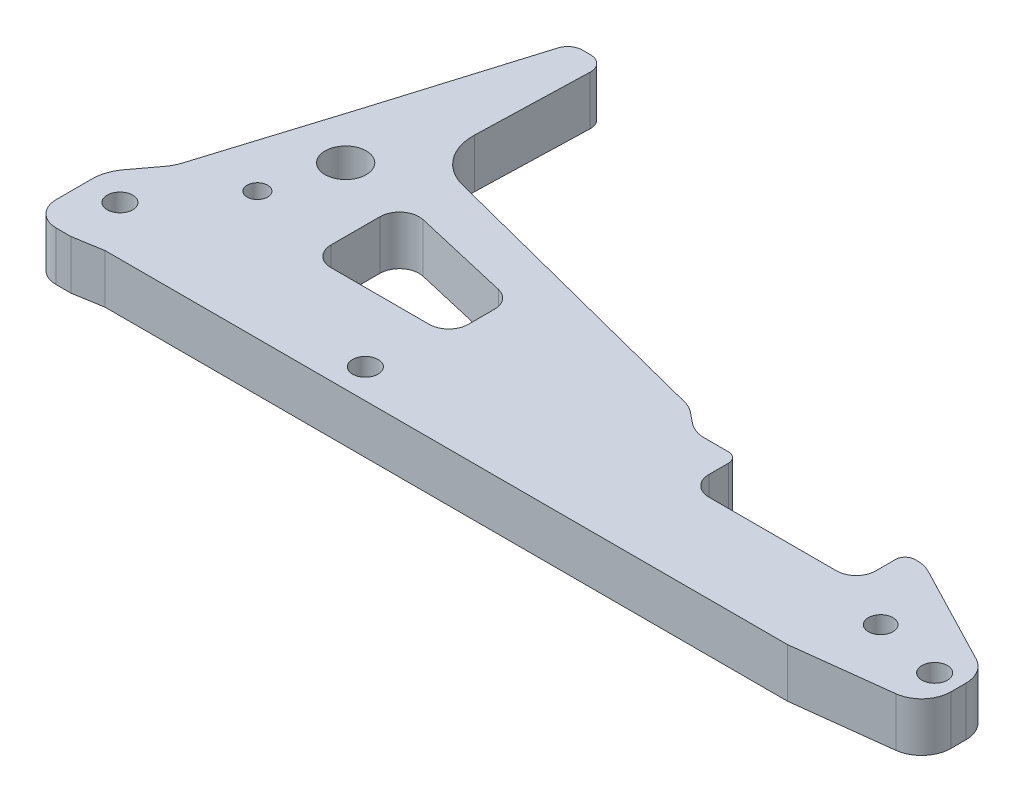
SolidWorks part; units mm, degrees
material "PE High Density"
ref_plane "Front Plane" through (0, 0, 0) normal (0, 0, 1) x (1, 0, 0)
ref_plane "Top Plane" through (0, 0, 0) normal (0, 1, 0) x (1, 0, 0)
ref_plane "Right Plane" through (0, 0, 0) normal (1, 0, 0) x (0, 0, -1)
sketch "Sketch1" plane through (0, 0, 0) normal (0, 1, 0) x (1, 0, 0)
  line L0 (164, 15) -> (139, 28)
  line L5 (164, 3) -> (139, 0)
  line L7 (-14, 14) -> (-14, 2)
  line L9 (0, 0) -> (139, 0)
  line L10 (164, 3) -> (164, 15)
  line L13 (92, 28) -> (139, 28)
  line L15 (1, 51) -> (11, 84)
  line L16 (11, 84) -> (18, 84)
  line L18 (-14, 2) -> (-14, -1)
  line L19 (-14, -1) -> (-6, -1)
  line L22 (-6, -1) -> (0, 0)
  line L23 (17, 50) -> (87, 32)
  line L24 (87, 32) -> (92, 28)
  line L25 (18, 84) -> (17, 50)
  line L26 (-14, 14) -> (-8, 22)
  line L27 (-8, 22) -> (1, 51)
  circle A0 centre (-7, 10) radius 2.6
  circle A3 centre (159, 10) radius 2.6
  circle A4 centre (5, 26) radius 2.1
  circle A6 centre (9, 40) radius 4.2
  circle A8 centre (145, 13) radius 2.5
  dimension "D9" = 5.2
  dimension "D12" = 5
  dimension "D15" = 16
  dimension "D13" = 5.2
  dimension "D17" = 4.2
  dimension "D20" = 6
  dimension "D23" = 8.4
  dimension "D27" = 10
  dimension "D3" = 44
  dimension "D4" = 3
  dimension "D5" = 25
  dimension "D6" = 25
  dimension "D7" = 166
  dimension "D8" = 12
  dimension "D10" = 7
  dimension "D11" = 8
  dimension "D14" = 40
  dimension "D16" = 5
  dimension "D18" = 7
  dimension "D19" = 12
  dimension "D21" = 10
  dimension "D22" = 75
  dimension "D24" = 18
  dimension "D25" = 15
  dimension "D26" = 16
  dimension "D28" = 12
  dimension "D29" = 10
  dimension "D30" = 3
  dimension "D31" = 8
  dimension "D32" = 70
  dimension "D33" = 16
  dimension "D34" = 14
  dimension "D35" = 6
  dimension "D36" = 8
  dimension "D37" = 29
  dimension "D38" = 4
  dimension "D39" = 28
  dimension "D40" = 13
extrude "Boss-Extrude1" add sketch "Sketch1" along normal blind 10
fillet "Fillet2" radius 6 3 edges at (164, 5, -3) (164, 5, -15) (139, 5, -28)
fillet "Fillet3" radius 3 2 edges at (11, 5, -84) (18, 5, -84)
sketch "Sketch4" plane through (0, 10, 0) normal (0, 1, 0) x (1, 0, 0)
  line L0 (22, 39) -> (22, 20)
  line L6 (22, 39) -> (50, 32.5)
  line L7 (50, 32.5) -> (50, 20)
  line L21 (50, 20) -> (22, 20)
  circle A0 centre (9, 40) radius 4.2 construction
  dimension "D1" = 13
  dimension "D2" = 1
  dimension "D3" = 19
  dimension "D5" = 28
  dimension "D8" = 12.5
extrude "Cut-Extrude1" cut sketch "Sketch4" against normal through all
sketch "Sketch7" plane through (0, 10, 0) normal (0, 1, 0) x (1, 0, 0)
  circle A0 centre (47, 6) radius 2.6
  circle A1 centre (9, 40) radius 4.2 construction
  dimension "D3" = 5.2
  dimension "D1" = 6
  dimension "D2" = 38
extrude "Cut-Extrude4" cut sketch "Sketch7" against normal through all
fillet "Fillet8" radius 5 1 edges at (-14, 5, 1)
fillet "Fillet9" radius 4 4 edges at (22, 5, -20) (50, 5, -32.5) (22, 5, -39) (50, 5, -20)
sketch "Sketch10" plane through (0, 10, 0) normal (0, 1, 0) x (1, 0, 0)
  line L0 (101, 28) -> (101, 18)
  line L1 (137.5332, 28) -> (92, 28) construction
  line L2 (101, 18) -> (135, 18)
  line L3 (135, 18) -> (135, 28)
  line L4 (135, 28) -> (101, 28)
  circle A0 centre (9, 40) radius 4.2 construction
  dimension "D3" = 92
  dimension "D1" = 10
  dimension "D2" = 0
  dimension "D4" = 34
extrude "Cut-Extrude6" cut sketch "Sketch10" against normal through all
fillet "Fillet10" radius 4 2 edges at (135, 5, -18) (101, 5, -18)
sketch "Sketch12" plane through (0, 0, 0) normal (0, 1, 0) x (1, 0, 0)
  line L4 (58, 37) -> (83, 31.0347)
  line L5 (83, 31.0347) -> (89, 26.0347)
  line L6 (89, 26.0347) -> (89, 14)
  line L7 (89, 14) -> (58, 14)
  line L8 (58, 14) -> (58, 37)
  line L9 (0, 0) -> (139, 0) construction
  circle A4 centre (-7, 10) radius 2.6 construction
  dimension "D3" = 65
  dimension "D5" = 14
  dimension "D6" = 23
  dimension "D7" = 25
  dimension "D8" = 5
  dimension "D9" = 6
extrude "Cut-Extrude7" cut sketch "Sketch12" along normal blind 5
fillet "Fillet14" radius 6 2 edges at (92, 5, -28) (87, 5, -32)
fillet "Fillet15" radius 2 2 edges at (101, 5, -28) (135, 5, -28)
fillet "Fillet16" radius 10 1 edges at (17, 5, -50)
fillet "Fillet17" radius 8 2 edges at (-8, 5, -22) (-14, 5, -14)
fillet "Fillet18" radius 4 5 edges at (83, 2.5, -31.0347) (89, 2.5, -26.0347) (89, 2.5, -14) (58, 2.5, -14) (58, 2.5, -37)
